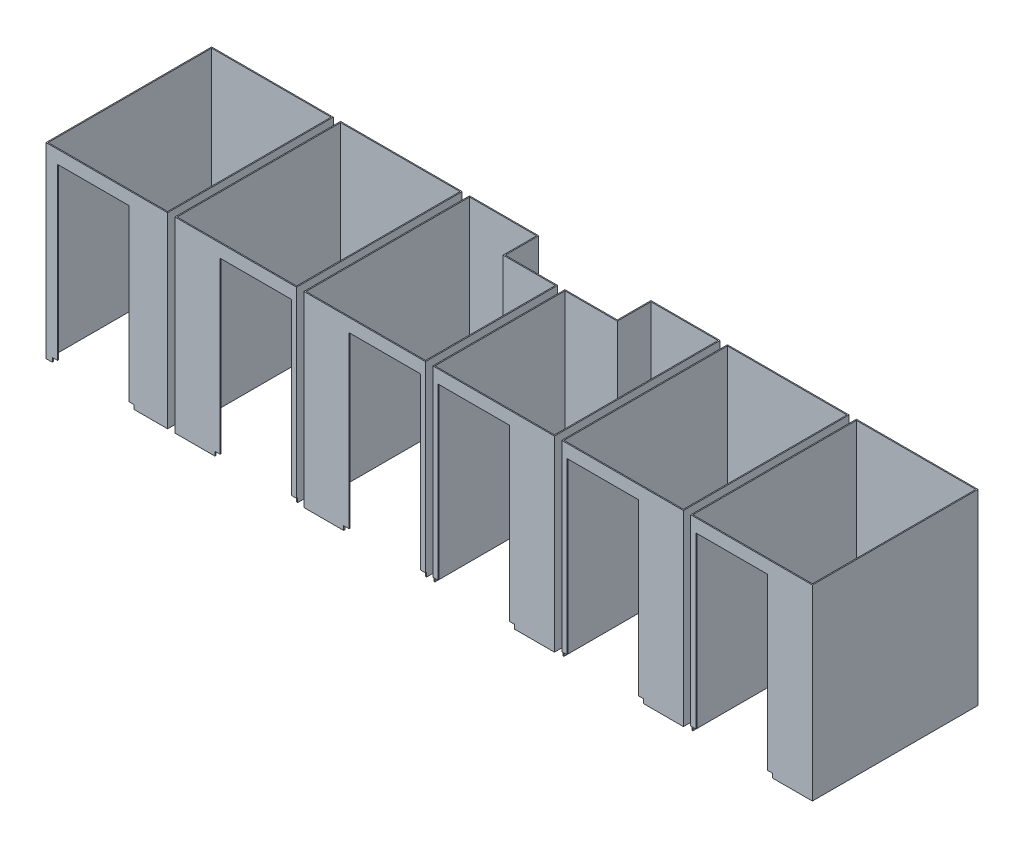
SolidWorks part; units mm, degrees
ref_plane "Front Plane" through (0, 0, 0) normal (0, 0, 1) x (1, 0, 0)
ref_plane "Top Plane" through (0, 0, 0) normal (0, 1, 0) x (1, 0, 0)
ref_plane "Right Plane" through (0, 0, 0) normal (1, 0, 0) x (0, 0, -1)
sketch "Sketch2" plane through (0, 0, 0) normal (0, 1, 0) x (1, 0, 0)
  line L4 (1612.9, 50.8) -> (3086.1, 50.8)
  line L5 (3086.1, 50.8) -> (3086.1, 2057.4)
  line L6 (3086.1, 2057.4) -> (1612.9, 2057.4)
  line L7 (1612.9, 2057.4) -> (1612.9, 50.8)
  line L8 (1612.9, 50.8) -> (3086.1, 50.8)
  line L9 (3086.1, 50.8) -> (3086.1, 2057.4)
  line L10 (3086.1, 2057.4) -> (1612.9, 2057.4)
  line L11 (1612.9, 2057.4) -> (1612.9, 50.8)
  line L12 (1524, 2057.4) -> (50.8, 2057.4)
  line L13 (50.8, 2057.4) -> (50.8, 50.8)
  line L14 (4013.2, 1651) -> (4013.2, 2057.4)
  line L15 (4648.2, 1651) -> (4013.2, 1651)
  line L16 (4648.2, 50.8) -> (4648.2, 1651)
  line L17 (3175, 50.8) -> (4648.2, 50.8)
  line L18 (3175, 2057.4) -> (3175, 50.8)
  line L19 (4013.2, 2057.4) -> (3175, 2057.4)
  line L20 (4013.2, 1651) -> (4013.2, 2057.4)
  line L21 (4648.2, 1651) -> (4013.2, 1651)
  line L22 (4648.2, 50.8) -> (4648.2, 1651)
  line L23 (3175, 50.8) -> (4648.2, 50.8)
  line L24 (3175, 2057.4) -> (3175, 50.8)
  line L25 (4013.2, 2057.4) -> (3175, 2057.4)
  line L26 (50.8, 50.8) -> (1524, 50.8)
  line L27 (1524, 50.8) -> (1524, 2057.4)
  line L28 (1524, 2057.4) -> (50.8, 2057.4)
  line L29 (50.8, 2057.4) -> (50.8, 50.8)
  line L30 (50.8, 50.8) -> (1524, 50.8)
  line L31 (1524, 50.8) -> (1524, 2057.4)
  line L32 (6299.2, 2057.4) -> (6299.2, 50.8)
  line L33 (7772.4, 2057.4) -> (6299.2, 2057.4)
  line L34 (7772.4, 50.8) -> (7772.4, 2057.4)
  line L35 (6299.2, 50.8) -> (7772.4, 50.8)
  line L36 (6299.2, 2057.4) -> (6299.2, 50.8)
  line L37 (7772.4, 2057.4) -> (6299.2, 2057.4)
  line L38 (7772.4, 50.8) -> (7772.4, 2057.4)
  line L39 (6299.2, 50.8) -> (7772.4, 50.8)
  line L40 (3073.4, 2044.7) -> (1625.6, 2044.7)
  line L41 (3073.4, 63.5) -> (3073.4, 2044.7)
  line L42 (5372.1, 2057.4) -> (5372.1, 1651)
  line L43 (6210.3, 2057.4) -> (5372.1, 2057.4)
  line L44 (6210.3, 50.8) -> (6210.3, 2057.4)
  line L45 (4737.1, 50.8) -> (6210.3, 50.8)
  line L46 (4737.1, 1651) -> (4737.1, 50.8)
  line L47 (5372.1, 1651) -> (4737.1, 1651)
  line L48 (5372.1, 2057.4) -> (5372.1, 1651)
  line L49 (6210.3, 2057.4) -> (5372.1, 2057.4)
  line L50 (6210.3, 50.8) -> (6210.3, 2057.4)
  line L51 (4737.1, 50.8) -> (6210.3, 50.8)
  line L52 (4737.1, 1651) -> (4737.1, 50.8)
  line L53 (5372.1, 1651) -> (4737.1, 1651)
  line L54 (1625.6, 63.5) -> (3073.4, 63.5)
  line L55 (1625.6, 2044.7) -> (1625.6, 63.5)
  line L56 (3073.4, 2044.7) -> (1625.6, 2044.7)
  line L57 (3073.4, 63.5) -> (3073.4, 2044.7)
  line L58 (1625.6, 63.5) -> (3073.4, 63.5)
  line L59 (1625.6, 2044.7) -> (1625.6, 63.5)
  line L60 (9334.5, 50.8) -> (9334.5, 2057.4)
  line L61 (7861.3, 50.8) -> (9334.5, 50.8)
  line L62 (7861.3, 2057.4) -> (7861.3, 50.8)
  line L63 (9334.5, 2057.4) -> (7861.3, 2057.4)
  line L64 (9334.5, 50.8) -> (9334.5, 2057.4)
  line L65 (7861.3, 50.8) -> (9334.5, 50.8)
  line L66 (7861.3, 2057.4) -> (7861.3, 50.8)
  line L67 (9334.5, 2057.4) -> (7861.3, 2057.4)
  line L68 (1511.3, 2044.7) -> (63.5, 2044.7)
  line L69 (1511.3, 63.5) -> (1511.3, 2044.7)
  line L70 (63.5, 63.5) -> (1511.3, 63.5)
  line L71 (63.5, 2044.7) -> (63.5, 63.5)
  line L72 (1511.3, 2044.7) -> (63.5, 2044.7)
  line L73 (1511.3, 63.5) -> (1511.3, 2044.7)
  line L74 (63.5, 63.5) -> (1511.3, 63.5)
  line L75 (63.5, 2044.7) -> (63.5, 63.5)
  line L76 (9321.8, 2044.7) -> (7874, 2044.7)
  line L77 (9321.8, 63.5) -> (9321.8, 2044.7)
  line L78 (7874, 63.5) -> (9321.8, 63.5)
  line L79 (7874, 2044.7) -> (7874, 63.5)
  line L80 (9321.8, 2044.7) -> (7874, 2044.7)
  line L81 (9321.8, 63.5) -> (9321.8, 2044.7)
  line L82 (7874, 63.5) -> (9321.8, 63.5)
  line L83 (7874, 2044.7) -> (7874, 63.5)
  line L84 (7759.7, 2044.7) -> (6311.9, 2044.7)
  line L85 (7759.7, 63.5) -> (7759.7, 2044.7)
  line L86 (6311.9, 63.5) -> (7759.7, 63.5)
  line L87 (6311.9, 2044.7) -> (6311.9, 63.5)
  line L88 (7759.7, 2044.7) -> (6311.9, 2044.7)
  line L89 (7759.7, 63.5) -> (7759.7, 2044.7)
  line L90 (6311.9, 63.5) -> (7759.7, 63.5)
  line L91 (6311.9, 2044.7) -> (6311.9, 63.5)
  line L94 (5384.8, 1638.3) -> (4749.8, 1638.3)
  line L95 (5384.8, 2044.7) -> (5384.8, 1638.3)
  line L96 (6197.6, 2044.7) -> (5384.8, 2044.7)
  line L97 (6197.6, 63.5) -> (6197.6, 2044.7)
  line L98 (4749.8, 63.5) -> (6197.6, 63.5)
  line L99 (4749.8, 1638.3) -> (4749.8, 63.5)
  line L100 (5384.8, 1638.3) -> (4749.8, 1638.3)
  line L101 (5384.8, 2044.7) -> (5384.8, 1638.3)
  line L102 (6197.6, 2044.7) -> (5384.8, 2044.7)
  line L103 (6197.6, 63.5) -> (6197.6, 2044.7)
  line L104 (4749.8, 63.5) -> (6197.6, 63.5)
  line L105 (4749.8, 1638.3) -> (4749.8, 63.5)
  line L106 (3187.7, 63.5) -> (4635.5, 63.5)
  line L107 (3187.7, 2044.7) -> (3187.7, 63.5)
  line L108 (4000.5, 2044.7) -> (3187.7, 2044.7)
  line L109 (4000.5, 1638.3) -> (4000.5, 2044.7)
  line L110 (4635.5, 1638.3) -> (4000.5, 1638.3)
  line L111 (4635.5, 63.5) -> (4635.5, 1638.3)
  line L112 (3187.7, 63.5) -> (4635.5, 63.5)
  line L113 (3187.7, 2044.7) -> (3187.7, 63.5)
  line L114 (4000.5, 2044.7) -> (3187.7, 2044.7)
  line L115 (4000.5, 1638.3) -> (4000.5, 2044.7)
  line L116 (4635.5, 1638.3) -> (4000.5, 1638.3)
  line L117 (4635.5, 63.5) -> (4635.5, 1638.3)
  dimension "D1" = 0
  dimension "D2" = 0
  dimension "D3" = 0
  dimension "D4" = 0
  dimension "D5" = 0
  dimension "D6" = 0
  dimension "D7" = 0
  dimension "D8" = 0
  dimension "D9" = 0
  dimension "D10" = 0
  dimension "D11" = 0
  dimension "D12" = 0
extrude "Boss-Extrude1" add sketch "Sketch2" along normal up to surface (2266.95 mm away)
sketch "Sketch3" plane through (0, 0, -50.8) normal (0, 0, 1) x (1, 0, 0)
  line L50 (127, 0) -> (1117.6, 0)
  line L51 (1054.1, 50.8) -> (1054.1, 2108.2)
  line L52 (1117.6, 0) -> (1117.6, 50.8)
  line L53 (1117.6, 50.8) -> (1054.1, 50.8)
  line L54 (127, 50.8) -> (127, 0)
  line L55 (190.5, 50.8) -> (127, 50.8)
  line L56 (190.5, 2108.2) -> (190.5, 50.8)
  line L57 (1054.1, 2108.2) -> (190.5, 2108.2)
  line L58 (127, 0) -> (1117.6, 0)
  line L59 (1054.1, 50.8) -> (1054.1, 2108.2)
  line L60 (1117.6, 0) -> (1117.6, 50.8)
  line L61 (1117.6, 50.8) -> (1054.1, 50.8)
  line L62 (127, 50.8) -> (127, 0)
  line L63 (190.5, 50.8) -> (127, 50.8)
  line L64 (190.5, 2108.2) -> (190.5, 50.8)
  line L65 (1054.1, 2108.2) -> (190.5, 2108.2)
  line L95 (2095.5, 0) -> (3086.1, 0)
  line L96 (2095.5, 0) -> (3086.1, 0)
  line L100 (2095.5, 50.8) -> (2095.5, 0)
  line L101 (2159, 50.8) -> (2095.5, 50.8)
  line L102 (3086.1, 0) -> (3086.1, 50.8)
  line L103 (3086.1, 50.8) -> (3022.6, 50.8)
  line L104 (3022.6, 50.8) -> (3022.6, 2108.2)
  line L105 (3022.6, 2108.2) -> (2159, 2108.2)
  line L106 (2159, 2108.2) -> (2159, 50.8)
  line L107 (2095.5, 50.8) -> (2095.5, 0)
  line L108 (2159, 50.8) -> (2095.5, 50.8)
  line L109 (3086.1, 0) -> (3086.1, 50.8)
  line L110 (3086.1, 50.8) -> (3022.6, 50.8)
  line L111 (3022.6, 50.8) -> (3022.6, 2108.2)
  line L112 (3022.6, 2108.2) -> (2159, 2108.2)
  line L113 (2159, 2108.2) -> (2159, 50.8)
  line L130 (3657.6, 50.8) -> (3657.6, 0)
  line L131 (3721.1, 50.8) -> (3657.6, 50.8)
  line L132 (4584.7, 50.8) -> (4584.7, 2108.2)
  line L133 (3721.1, 2108.2) -> (3721.1, 50.8)
  line L134 (4584.7, 2108.2) -> (3721.1, 2108.2)
  line L135 (3657.6, 50.8) -> (3657.6, 0)
  line L136 (3721.1, 50.8) -> (3657.6, 50.8)
  line L137 (4584.7, 50.8) -> (4584.7, 2108.2)
  line L138 (3721.1, 2108.2) -> (3721.1, 50.8)
  line L139 (4584.7, 2108.2) -> (3721.1, 2108.2)
  line L144 (4648.2, 0) -> (4648.2, 50.8)
  line L145 (4648.2, 50.8) -> (4584.7, 50.8)
  line L146 (3657.6, 0) -> (4648.2, 0)
  line L147 (4648.2, 0) -> (4648.2, 50.8)
  line L148 (4648.2, 50.8) -> (4584.7, 50.8)
  line L149 (3657.6, 0) -> (4648.2, 0)
  line L191 (4800.6, 50.8) -> (4737.1, 50.8)
  line L192 (4737.1, 50.8) -> (4737.1, 0)
  line L193 (4737.1, 0) -> (5727.7, 0)
  line L194 (5727.7, 0) -> (5727.7, 50.8)
  line L195 (5727.7, 50.8) -> (5664.2, 50.8)
  line L196 (5664.2, 50.8) -> (5664.2, 2108.2)
  line L197 (4800.6, 2108.2) -> (4800.6, 50.8)
  line L198 (5664.2, 2108.2) -> (4800.6, 2108.2)
  line L199 (4800.6, 50.8) -> (4737.1, 50.8)
  line L200 (4737.1, 50.8) -> (4737.1, 0)
  line L201 (4737.1, 0) -> (5727.7, 0)
  line L202 (5727.7, 0) -> (5727.7, 50.8)
  line L203 (5727.7, 50.8) -> (5664.2, 50.8)
  line L204 (5664.2, 50.8) -> (5664.2, 2108.2)
  line L205 (4800.6, 2108.2) -> (4800.6, 50.8)
  line L206 (5664.2, 2108.2) -> (4800.6, 2108.2)
  line L243 (6299.2, 50.8) -> (6299.2, 0)
  line L244 (6362.7, 50.8) -> (6299.2, 50.8)
  line L245 (6299.2, 0) -> (7289.8, 0)
  line L246 (7289.8, 0) -> (7289.8, 50.8)
  line L247 (7289.8, 50.8) -> (7226.3, 50.8)
  line L248 (7226.3, 50.8) -> (7226.3, 2108.2)
  line L249 (6362.7, 2108.2) -> (6362.7, 50.8)
  line L250 (7226.3, 2108.2) -> (6362.7, 2108.2)
  line L251 (6299.2, 50.8) -> (6299.2, 0)
  line L252 (6362.7, 50.8) -> (6299.2, 50.8)
  line L253 (6299.2, 0) -> (7289.8, 0)
  line L254 (7289.8, 0) -> (7289.8, 50.8)
  line L255 (7289.8, 50.8) -> (7226.3, 50.8)
  line L256 (7226.3, 50.8) -> (7226.3, 2108.2)
  line L257 (6362.7, 2108.2) -> (6362.7, 50.8)
  line L258 (7226.3, 2108.2) -> (6362.7, 2108.2)
  line L295 (7861.3, 50.8) -> (7861.3, 0)
  line L296 (7924.8, 50.8) -> (7861.3, 50.8)
  line L297 (7861.3, 0) -> (8851.9, 0)
  line L298 (8851.9, 0) -> (8851.9, 50.8)
  line L299 (8851.9, 50.8) -> (8788.4, 50.8)
  line L300 (8788.4, 50.8) -> (8788.4, 2108.2)
  line L301 (7924.8, 2108.2) -> (7924.8, 50.8)
  line L302 (8788.4, 2108.2) -> (7924.8, 2108.2)
  line L303 (7861.3, 50.8) -> (7861.3, 0)
  line L304 (7924.8, 50.8) -> (7861.3, 50.8)
  line L305 (7861.3, 0) -> (8851.9, 0)
  line L306 (8851.9, 0) -> (8851.9, 50.8)
  line L307 (8851.9, 50.8) -> (8788.4, 50.8)
  line L308 (8788.4, 50.8) -> (8788.4, 2108.2)
  line L309 (7924.8, 2108.2) -> (7924.8, 50.8)
  line L310 (8788.4, 2108.2) -> (7924.8, 2108.2)
  dimension "D1" = 0
  dimension "D2" = 0
  dimension "D3" = 0
  dimension "D4" = 0
  dimension "D5" = 0
  dimension "D6" = 0
  dimension "D7" = 0
  dimension "D8" = 0
extrude "Cut-Extrude1" cut sketch "Sketch3" against normal up to vertex (12.7 mm away)
